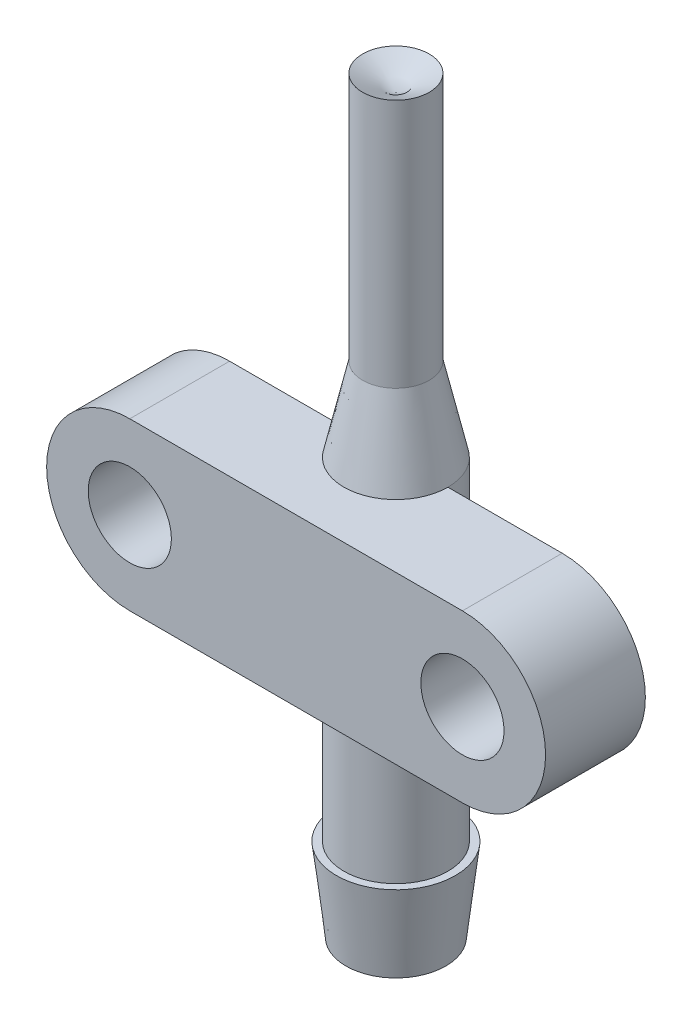
SolidWorks part; units mm, degrees
ref_plane "Front Plane" through (0, 0, 0) normal (0, 0, 1) x (1, 0, 0)
ref_plane "Top Plane" through (0, 0, 0) normal (0, 1, 0) x (1, 0, 0)
ref_plane "Right Plane" through (0, 0, 0) normal (1, 0, 0) x (0, 0, -1)
sketch "Sketch1" plane through (0, 0, 0) normal (0, 0, 1) x (1, 0, 0)
  line L0 (2, 30) -> (3.125, 25)
  line L1 (0, 44) -> (2, 45)
  line L2 (2, 45) -> (2, 30)
  line L3 (3.125, 25) -> (3.125, 5)
  line L4 (3.125, 5) -> (3.575, 5)
  line L5 (3, 0) -> (1.75, 0)
  line L6 (3.575, 5) -> (3, 0)
  line L10 (0, 44) -> (0, 40)
  line L11 (1, 30) -> (1.75, 25)
  line L12 (1.75, 25) -> (1.75, 0)
  line L13 (0, 0) -> (0, 44) construction
  line L14 (0, 40) -> (1, 40)
  line L15 (1, 30) -> (1, 40)
  point P1 (0, 0)
  dimension "D1" = 4
  dimension "D2" = 15
  dimension "D3" = 1
  dimension "D4" = 1
  dimension "D5" = 4
  dimension "D6" = 5
  dimension "D7" = 20
  dimension "D8" = 3.5
  dimension "D9" = 7.15
  dimension "D10" = 6
  dimension "D11" = 6.25
  dimension "D12" = 5
revolve "Revolve1" add sketch "Sketch1" angle 360 about L13
sketch "Sketch2" plane through (0, 0, 0) normal (0, 0, 1) x (1, 0, 0)
  line L0 (-10, 20) -> (10, 20) construction
  line L1 (-10, 25) -> (10, 25)
  line L2 (-10, 15) -> (10, 15)
  line L3 (3.125, 25) -> (-3.125, 25) construction
  arc A0 (-10, 25) -> (-10, 15) centre (-10, 20) ccw
  arc A1 (10, 15) -> (10, 25) centre (10, 20) ccw
  circle A2 centre (-10, 20) radius 2.5
  circle A3 centre (10, 20) radius 2.5
  point P2 (0, 20)
  dimension "D1" = 5
  dimension "D3" = 20
  dimension "D2" = 10
extrude "Boss-Extrude1" add sketch "Sketch2" along normal blind 6 separate body
sketch "Sketch3" plane through (0, 0, 0) normal (0, -1, 0) x (1, 0, 0)
  circle A0 centre (0, 0) radius 1.75 construction
  circle A1 centre (0, 0) radius 1.75
extrude "Cut-Extrude1" cut sketch "Sketch3" against normal up to surface (25 mm away) up to face at (0, 25, 3)
